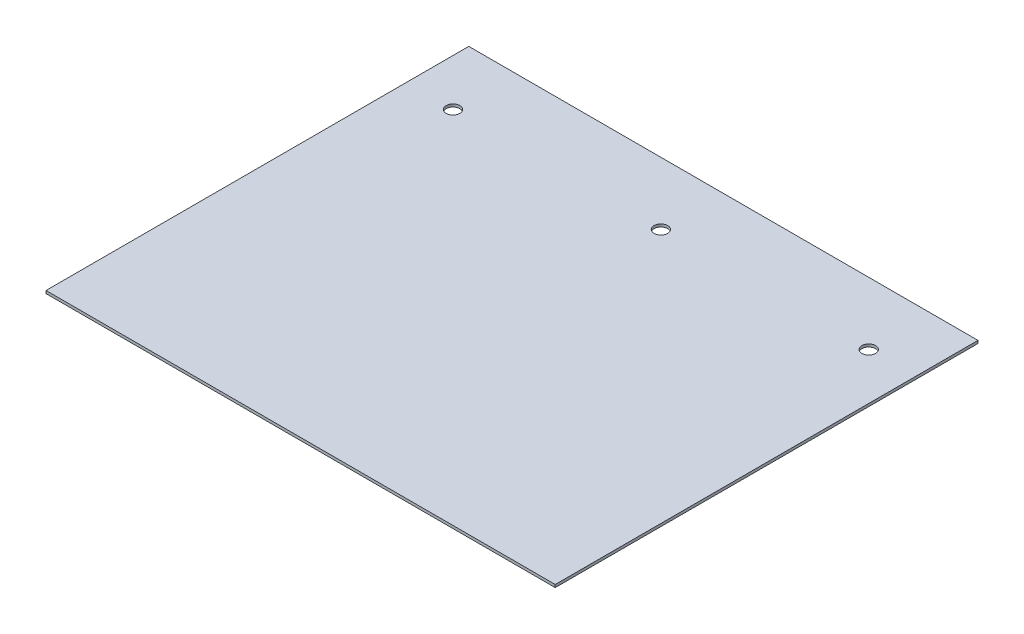
SolidWorks part; units mm, degrees
ref_plane "Front Plane" through (0, 0, 0) normal (0, 0, 1) x (1, 0, 0)
ref_plane "Top Plane" through (0, 0, 0) normal (0, 1, 0) x (1, 0, 0)
ref_plane "Right Plane" through (0, 0, 0) normal (1, 0, 0) x (0, 0, -1)
sketch "Sketch1" plane through (0, 0, 0) normal (0, 1, 0) x (1, 0, 0)
  line L0 (93.345, -199.9996) -> (93.345, -67.9196) construction
  line L1 (0, 0) -> (186.69, 0)
  line L2 (0, 0) -> (0, -199.9996)
  line L3 (0, -199.9996) -> (186.69, -199.9996)
  line L4 (186.69, 0) -> (186.69, -199.9996)
  line L5 (93.345, -67.9196) -> (186.69, -67.9196) construction
  line L6 (93.345, -67.9196) -> (0, -67.9196) construction
  circle A0 centre (93.345, -67.9196) radius 2.5
  circle A1 centre (17.145, -67.9196) radius 2.5
  circle A2 centre (93.345, -67.9196) radius 2.5
  circle A3 centre (169.545, -67.9196) radius 2.5
  dimension "D4" = 5
  dimension "D1" = 199.9996
  dimension "D2" = 186.69
  dimension "D3" = 132.08
  dimension "D5" = 2
  dimension "D6" = 2
extrude "Boss-Extrude1" add sketch "Sketch1" against normal blind 1 contours L4 L1 L2 L3 A3 A1 A0
ref_plane "Plane1" through (93.345, 0, 0) normal (-1, 0, 0) x (0, 0, 1)
ref_plane "Plane2" through (0, 0, 99.9998) normal (0, 0, -1) x (-1, 0, 0)
ref_plane "Plane3" through (0, 0, 67.9196) normal (0, 0, 1) x (1, 0, 0)
sketch "Sketch2" plane through (0, 0, 0) normal (0, 1, 0) x (1, 0, 0)
  line L0 (186.69, 0) -> (186.69, -199.9996) construction
  line L1 (0, 0) -> (186.69, 0)
  line L2 (0, 0) -> (0, -45)
  line L3 (0, -45) -> (186.69, -45)
  line L4 (186.69, 0) -> (186.69, -45)
  dimension "D1" = 45
extrude "Cut-Extrude1" cut sketch "Sketch2" against normal through all both
